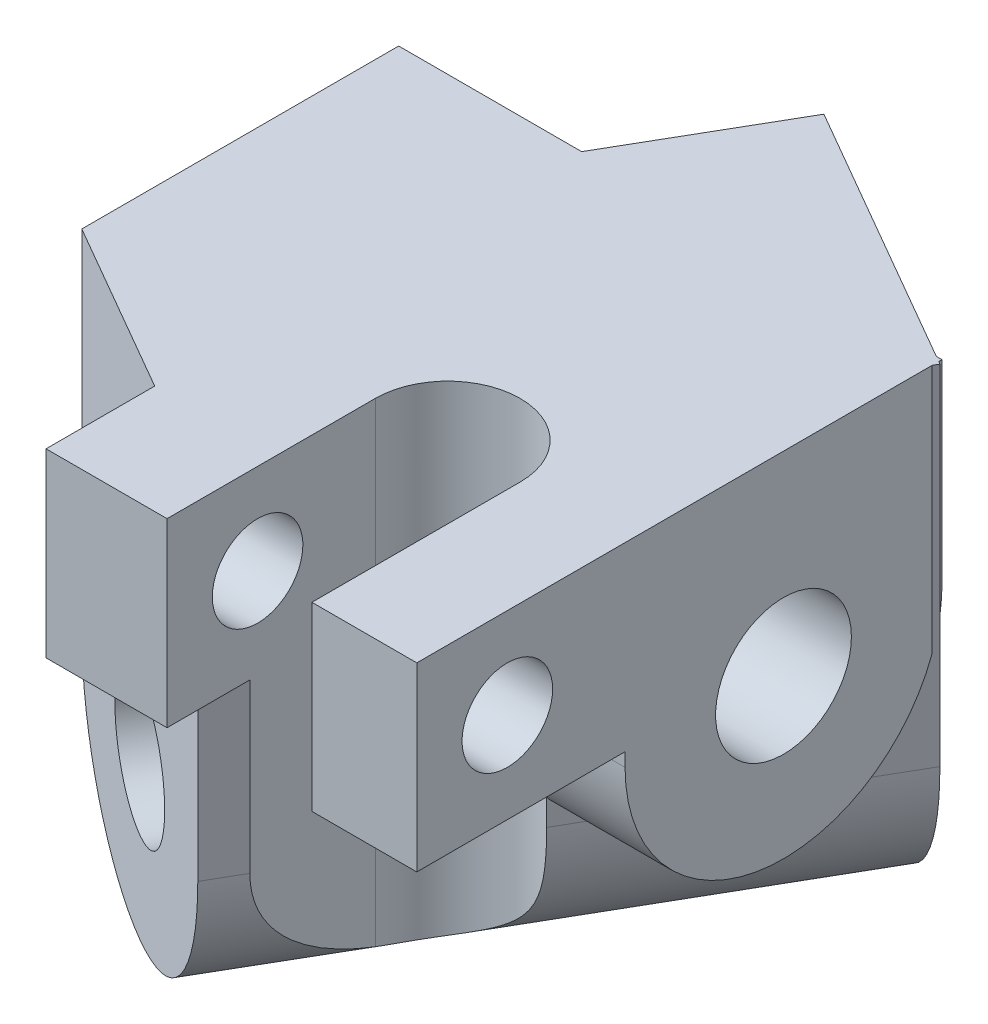
SolidWorks part; units mm, degrees
ref_plane "Front Plane" through (0, 0, 0) normal (0, 0, 1) x (1, 0, 0)
ref_plane "Top Plane" through (0, 0, 0) normal (0, 1, 0) x (1, 0, 0)
ref_plane "Right Plane" through (0, 0, 0) normal (1, 0, 0) x (0, 0, -1)
sketch "Sketch1" plane through (0, 0, 0) normal (1, 0, 0) x (0, 0, -1)
  line L0 (-8.75, 0) -> (8.75, 0)
  line L1 (8.75, 0) -> (8.75, 10.75)
  line L2 (-8.75, 10.75) -> (-8.75, 0)
  arc A0 (8.75, 10.75) -> (-8.75, 10.75) centre (0, 10.75) ccw
  circle A1 centre (0, 10.75) radius 3.75
  dimension "D1" = 8.75
  dimension "D3" = 7.5
  dimension "D2" = 7
extrude "Boss-Extrude1" add sketch "Sketch1" along normal blind 30
ref_plane "Plane1" through (-3.7889, 0, 6.5625) normal (0.5, 0, -0.866) x (-0.866, 0, -0.5)
sketch "Sketch2" plane through (-3.7889, 0, 6.5625) normal (0.5, 0, -0.866) x (-0.866, 0, -0.5)
  line L0 (-4.375, 0) -> (-4.375, 19.25)
  line L1 (-21.875, 19.25) -> (-21.875, 0)
  line L2 (-30.3558, 0) -> (-4.375, 0) construction
  line L3 (-21.875, 0) -> (-4.375, 0)
  line L4 (0, 14.5) -> (-31.5247, 14.5) construction
  arc A0 (-4.375, 19.25) -> (-21.875, 19.25) centre (-13.125, 19.25) ccw
  circle A1 centre (-13.125, 19.25) radius 3.75
  ellipse E0 centre (0, 10.75) end of major axis (0, 14.5) minor radius 1.875 construction
  ellipse E1 centre (0, 10.75) end of major axis (0, 14.5) minor radius 1.875 construction
  dimension "D1" = 8.75
  dimension "D2" = 7.5
  dimension "D3" = 1
extrude "Boss-Extrude2" add sketch "Sketch2" along normal blind 30
sketch "Sketch3" plane through (0, 0, 0) normal (0, -1, 0) x (1, 0, 0)
  line L1 (17.3205, 3.75) -> (10.8253, 15) construction
  line L3 (20.2073, 8.75) -> (15.1554, 17.5) construction
  line L4 (17.3205, 3.75) -> (30, 3.75) construction
  line L5 (30, 8.75) -> (30, -8.2115) construction
  line L6 (30, 8.75) -> (20.2073, 8.75) construction
  line L7 (-7.9566, 4.1562) -> (0.3789, 8.9687) construction
  line L8 (24.2073, 8.75) -> (24.2073, 15.6782)
  line L9 (16.2073, 15.6782) -> (24.2073, 15.6782)
  line L10 (16.2073, 15.6782) -> (16.2073, 8.75)
  arc A0 (16.2073, 8.75) -> (24.2073, 8.75) centre (20.2073, 8.75) ccw
  dimension "D1" = 8
  dimension "D2" = 5
  dimension "D3" = 5
extrude "Cut-Extrude1" cut sketch "Sketch3" against normal through all
sketch "Sketch4" plane through (0, 0, 0) normal (0, -1, 0) x (1, 0, 0)
  line L0 (24.2073, 8.75) -> (24.2073, 20.25)
  line L1 (24.2073, 20.25) -> (30, 20.25)
  line L2 (30, 20.25) -> (30, 8.75)
  line L3 (30, 8.75) -> (24.2073, 8.75)
  arc A0 (16.2073, 8.75) -> (24.2073, 8.75) centre (20.2073, 8.75) ccw construction
  arc A1 (16.2073, 8.75) -> (24.2073, 8.75) centre (20.2073, 8.75) ccw construction
  circle A2 centre (20.2073, 8.75) radius 4 construction
  dimension "D1" = 7.5
extrude "Boss-Extrude3" add sketch "Sketch4" against normal blind 10
sketch "Sketch6" plane through (0, 0, 0) normal (0, -1, 0) x (1, 0, 0)
  line L0 (16.2073, 15.6782) -> (16.2073, 20.25)
  line L1 (16.2073, 20.25) -> (9.5263, 20.25)
  line L2 (9.5263, 20.25) -> (9.5263, 14.25)
  line L3 (15.1554, 17.5) -> (0, 8.75) construction
  line L4 (30, 20.25) -> (24.2073, 20.25) construction
  line L5 (9.5263, 14.25) -> (16.2073, 15.6782)
  dimension "D1" = 6
extrude "Boss-Extrude4" add sketch "Sketch6" against normal up to surface (10 mm away) up to face at (27.1036, 10, 14.5)
sketch "Sketch5" plane through (30, 0, 0) normal (1, 0, 0) x (0, 0, -1)
  line L0 (-14.9644, 5) -> (-9.1409, 5) construction
  line L3 (-15.3741, 10) -> (-10.3407, 10) construction
  line L4 (-14.9644, 0) -> (-9.931, 0) construction
  line L5 (-20.25, 0) -> (8.2115, 0) construction
  line L6 (-20.25, 10) -> (-20.25, 0) construction
  circle A0 centre (-15.25, 5) radius 2.5
  dimension "D1" = 5
  dimension "D2" = 5
  dimension "D3" = 10
extrude "Cut-Extrude2" cut sketch "Sketch5" against normal through all
sketch "Sketch7" plane through (0, 0, 0) normal (-1, 0, 0) x (0, 0, 1)
  circle A0 centre (0, 10.75) radius 3.75 construction
  circle A1 centre (0, 10.75) radius 3.75
extrude "Cut-Extrude3" cut sketch "Sketch7" against normal through all
sketch "Sketch8" plane through (-3.7889, 0, 6.5625) normal (-0.5, 0, 0.866) x (0.866, 0, 0.5)
  circle A0 centre (13.125, 19.25) radius 3.75 construction
  circle A1 centre (13.125, 19.25) radius 3.75
extrude "Cut-Extrude4" cut sketch "Sketch8" against normal through all
mirror "Mirror1" about plane through (30, 0, 8.75) normal (0, 1, 0) of bodies 108
delete or keep bodies "Body-Delete1" type delete bodies bodies 108
